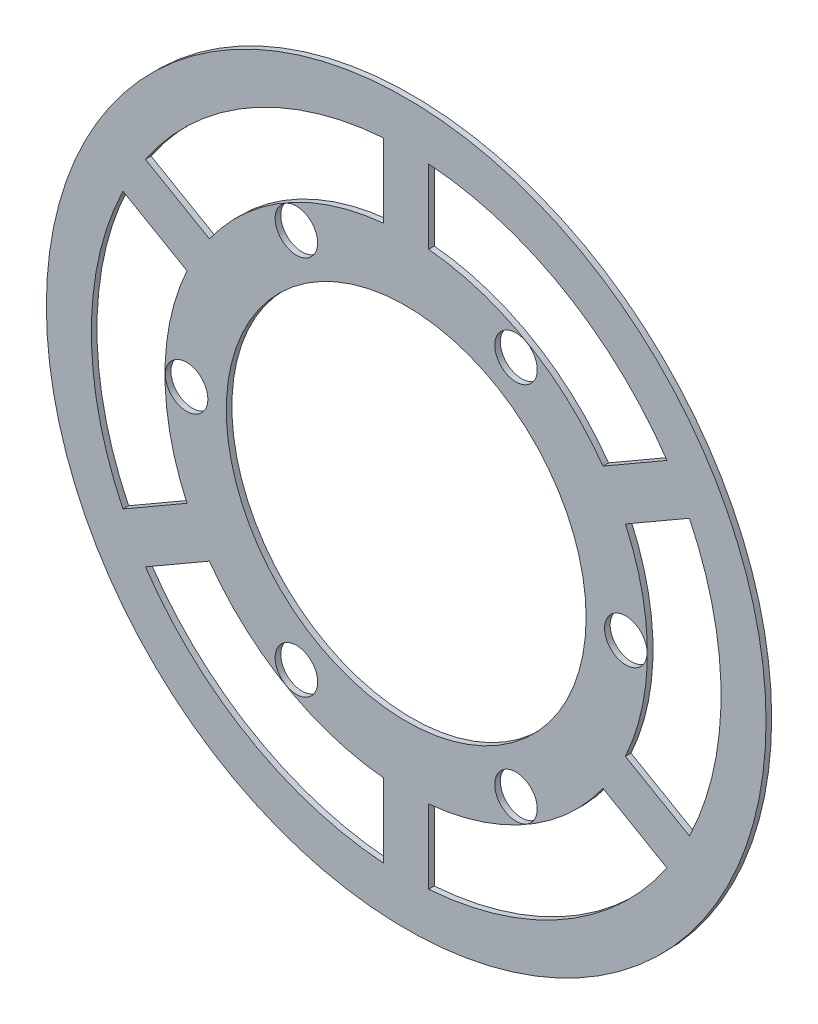
SolidWorks part; units mm, degrees
material "BUTYL"
ref_plane "Front Plane" through (0, 0, 0) normal (0, 0, 1) x (1, 0, 0)
ref_plane "Top Plane" through (0, 0, 0) normal (0, 1, 0) x (1, 0, 0)
ref_plane "Right Plane" through (0, 0, 0) normal (1, 0, 0) x (0, 0, -1)
sketch "Sketch1" plane through (0, 0, 0) normal (0, 0, 1) x (1, 0, 0)
  line L1 (-1.5844, 16.926) -> (-1.5844, 22.1685)
  line L2 (1.5844, 16.926) -> (1.5844, 22.1685)
  line L5 (13.8662, 9.8351) -> (18.4062, 12.4564)
  line L6 (15.4505, 7.0909) -> (19.9906, 9.7121)
  line L9 (-15.4505, 7.0909) -> (-19.9906, 9.7121)
  line L10 (-13.8662, 9.8351) -> (-18.4062, 12.4564)
  line L13 (-15.4505, -7.0909) -> (-19.9906, -9.7121)
  line L14 (-13.8662, -9.8351) -> (-18.4062, -12.4564)
  line L17 (-1.5844, -16.926) -> (-1.5844, -22.1685)
  line L18 (1.5844, -16.926) -> (1.5844, -22.1685)
  line L21 (13.8662, -9.8351) -> (18.4062, -12.4564)
  line L22 (15.4505, -7.0909) -> (19.9906, -9.7121)
  arc A0 (-15.4505, 7.0909) -> (-15.4505, -7.0909) centre (0, 0) ccw construction
  circle A1 centre (-15.5, 0) radius 1.5
  circle A2 centre (-7.75, 13.4234) radius 1.5
  circle A3 centre (7.75, 13.4234) radius 1.5
  circle A4 centre (15.5, 0) radius 1.5
  circle A5 centre (7.75, -13.4234) radius 1.5
  circle A6 centre (-7.75, -13.4234) radius 1.5
  arc A7 (-15.4735, 7.1025) -> (-15.4735, -7.1025) centre (0, 0) ccw
  arc A8 (-11.7048, 4.9283) -> (-11.7048, -4.9283) centre (0, 0) ccw
  arc A10 (1.5844, 16.926) -> (1.5858, 16.9517) centre (0, 17.0257) ccw
  arc A12 (13.8877, 9.8492) -> (13.8662, 9.8351) centre (14.7447, 8.5128) ccw
  arc A14 (13.8662, -9.8351) -> (13.8877, -9.8492) centre (14.7447, -8.5128) ccw
  arc A16 (1.5858, -16.9517) -> (1.5844, -16.926) centre (0, -17.0257) ccw
  arc A18 (-15.4505, -7.0909) -> (-15.4735, -7.1025) centre (-14.7447, -8.5128) ccw
  arc A20 (-13.8662, 9.8351) -> (-13.8877, 9.8492) centre (-14.7447, 8.5128) ccw
  arc A22 (-1.5844, 12.6008) -> (-10.1204, 7.6725) centre (0, 0) ccw
  arc A23 (-1.5858, 16.9517) -> (-13.8877, 9.8492) centre (0, 0) ccw
  arc A24 (-1.5844, 16.926) -> (-13.8662, 9.8351) centre (0, 0) ccw construction
  arc A25 (13.8877, 9.8492) -> (1.5858, 16.9517) centre (0, 0) ccw
  arc A26 (13.8662, 9.8351) -> (1.5844, 16.926) centre (0, 0) ccw construction
  arc A27 (10.1204, 7.6725) -> (1.5844, 12.6008) centre (0, 0) ccw
  arc A28 (11.7048, -4.9283) -> (11.7048, 4.9283) centre (0, 0) ccw
  arc A29 (15.4505, -7.0909) -> (15.4505, 7.0909) centre (0, 0) ccw construction
  arc A30 (15.4735, -7.1025) -> (15.4735, 7.1025) centre (0, 0) ccw
  arc A31 (-13.8662, -9.8351) -> (-1.5844, -16.926) centre (0, 0) ccw construction
  arc A32 (-13.8877, -9.8492) -> (-1.5858, -16.9517) centre (0, 0) ccw
  arc A33 (-10.1204, -7.6725) -> (-1.5844, -12.6008) centre (0, 0) ccw
  arc A34 (1.5844, -12.6008) -> (10.1204, -7.6725) centre (0, 0) ccw
  arc A35 (1.5844, -16.926) -> (13.8662, -9.8351) centre (0, 0) ccw construction
  arc A36 (1.5858, -16.9517) -> (13.8877, -9.8492) centre (0, 0) ccw
  arc A37 (-1.5858, 16.9517) -> (-1.5844, 16.926) centre (0, 17.0257) ccw
  arc A38 (15.4505, 7.0909) -> (15.4735, 7.1025) centre (14.7447, 8.5128) ccw
  arc A39 (15.4735, -7.1025) -> (15.4505, -7.0909) centre (14.7447, -8.5128) ccw
  arc A40 (-1.5844, -16.926) -> (-1.5858, -16.9517) centre (0, -17.0257) ccw
  arc A41 (-13.8877, -9.8492) -> (-13.8662, -9.8351) centre (-14.7447, -8.5128) ccw
  arc A42 (-15.4735, 7.1025) -> (-15.4505, 7.0909) centre (-14.7447, 8.5128) ccw
  arc A43 (-15.4729, 7.1038) -> (-15.4729, -7.1038) centre (0, 0) ccw
  circle A44 centre (0, 0) radius 12.7
  arc A45 (-19.9906, 9.7121) -> (-19.9906, -9.7121) centre (0, 0) ccw
  arc A46 (-1.5844, 16.9518) -> (-13.8885, 9.848) centre (0, 0) ccw
  arc A47 (13.8885, 9.848) -> (1.5844, 16.9518) centre (0, 0) ccw
  arc A48 (15.4729, -7.1038) -> (15.4729, 7.1038) centre (0, 0) ccw
  arc A49 (1.5844, -16.9518) -> (13.8885, -9.848) centre (0, 0) ccw
  arc A50 (-13.8885, -9.848) -> (-1.5844, -16.9518) centre (0, 0) ccw
  circle A51 centre (0, 0) radius 25.4
  arc A52 (-1.5844, 22.1685) -> (-18.4062, 12.4564) centre (0, 0) ccw
  arc A53 (18.4062, 12.4564) -> (1.5844, 22.1685) centre (0, 0) ccw
  arc A54 (19.9906, -9.7121) -> (19.9906, 9.7121) centre (0, 0) ccw
  arc A55 (1.5844, -22.1685) -> (18.4062, -12.4564) centre (0, 0) ccw
  arc A56 (-18.4062, -12.4564) -> (-1.5844, -22.1685) centre (0, 0) ccw
  dimension "D1" = 3
  dimension "D2" = 34
  dimension "D4" = 25.4
  dimension "D5" = 44.45
  dimension "D6" = 50.8
  dimension "D7" = 3.175
  dimension "D8" = 34.0514
  dimension "D3" = 6
  dimension "D9" = 6
extrude "Boss-Extrude1" add sketch "Sketch1" along normal blind 0.3969 contours A0 A6 A5 A4 A3 A2 A1
